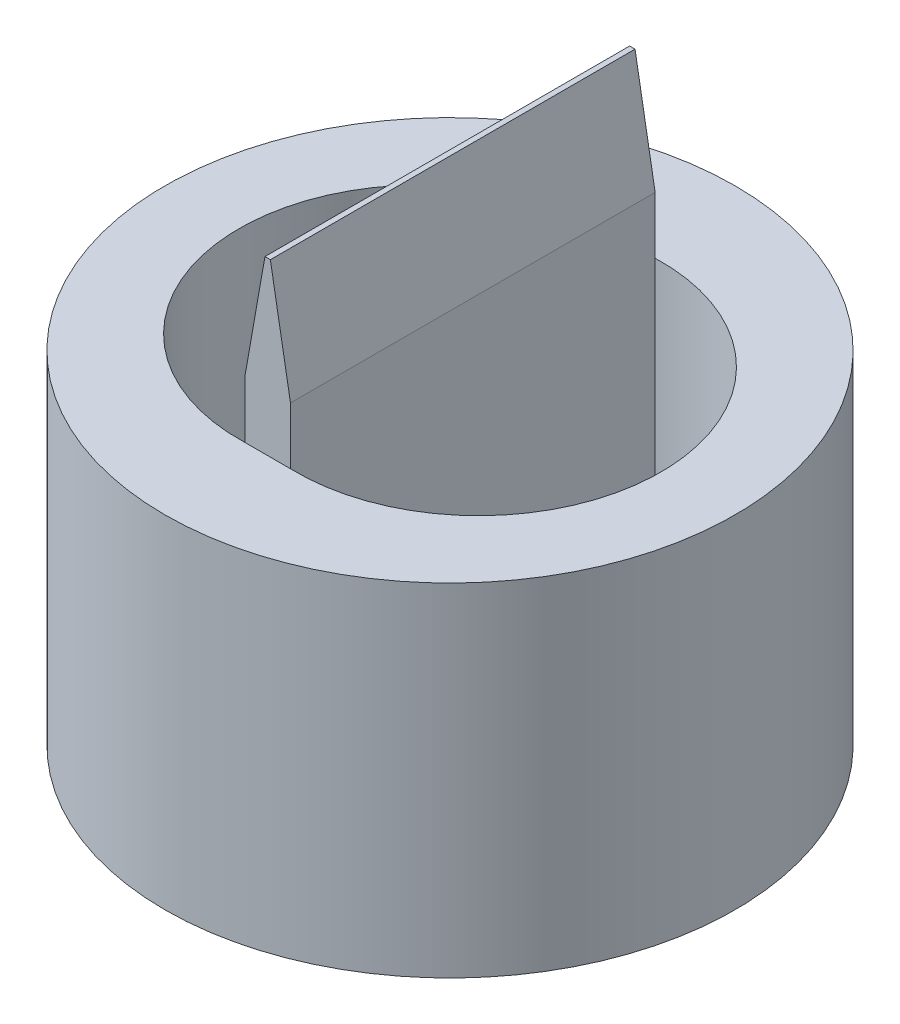
SolidWorks part; units mm, degrees
ref_plane "Спереди" through (0, 0, 0) normal (0, 0, 1) x (1, 0, 0)
ref_plane "Сверху" through (0, 0, 0) normal (0, 1, 0) x (1, 0, 0)
ref_plane "Справа" through (0, 0, 0) normal (1, 0, 0) x (0, 0, -1)
sketch "Эскиз1" plane through (0, 0, 0) normal (0, 1, 0) x (1, 0, 0)
  circle A0 centre (0, 0) radius 5
  dimension "D1" = 10
extrude "Бобышка-Вытянуть1" add sketch "Эскиз1" along normal blind 6
sketch "Эскиз2" plane through (0, 6, 0) normal (0, 1, 0) x (1, 0, 0)
  line L0 (-0.4, 3.1984) -> (-0.4, -3.1984)
  line L1 (0.4, -3.1984) -> (0.4, 3.1984)
  line L2 (-0.4, 3.1984) -> (0.4, -3.1984) construction
  line L3 (-0.4, -3.1984) -> (0.4, 3.1984) construction
  line L4 (0.4997, 0) -> (-0.4997, 0) construction
  line L5 (0, 5) -> (0, -5) construction
  circle A0 centre (0, 0) radius 5 construction
  arc A1 (-0.4, -3.1984) -> (-0.4, 3.1984) centre (-0.4997, 0) cw
  arc A2 (0.4, 3.1984) -> (0.4, -3.1984) centre (0.4997, 0) cw
  point P9 (0, 0)
  point P10 (0, 0)
  dimension "D1" = 3.2
  dimension "D2" = 0.8
extrude "Вырез-Вытянуть1" cut sketch "Эскиз2" against normal blind 4
sketch "Эскиз3" plane through (0, 6, 0) normal (0, 1, 0) x (1, 0, 0)
  line L1 (-0.4, -3.1984) -> (0.4, -3.1984)
  line L2 (-0.4, -3.1984) -> (-0.4, 3.1984)
  line L3 (-0.4, 3.1984) -> (0.4, 3.1984)
  line L4 (0.4, -3.1984) -> (0.4, 3.1984)
  point P0 (0, 0)
extrude "Бобышка-Вытянуть2" add sketch "Эскиз3" along normal blind 3
chamfer "Фаска1" distance 2 angle 10 2 edges at (-0.4, 9, 0) (0.4, 9, 0)
